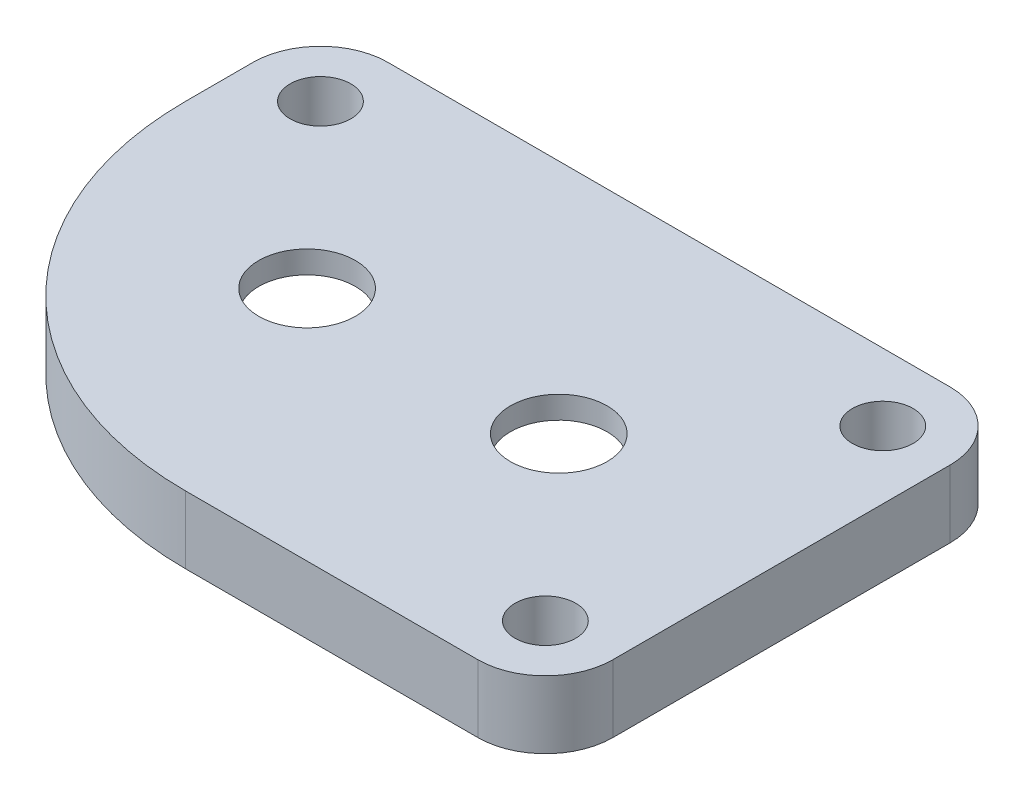
SolidWorks part; units mm, degrees
ref_plane "Front Plane" through (0, 0, 0) normal (0, 0, 1) x (1, 0, 0)
ref_plane "Top Plane" through (0, 0, 0) normal (0, 1, 0) x (1, 0, 0)
ref_plane "Right Plane" through (0, 0, 0) normal (1, 0, 0) x (0, 0, -1)
sketch "Sketch1" plane through (0, 0, 0) normal (0, 1, 0) x (1, 0, 0)
  line L0 (11.19, 0) -> (0, 0) construction
  line L2 (5.095, -10.5) -> (18.095, -10.5)
  line L3 (-9.905, 4.5) -> (-9.905, 7.5)
  line L4 (-6.905, 10.5) -> (18.095, 10.5)
  line L5 (21.095, -7.5) -> (21.095, 7.5)
  line L6 (-9.905, -10.5) -> (21.095, 10.5) construction
  line L7 (-9.905, 10.5) -> (21.095, -10.5) construction
  circle A0 centre (0, 0) radius 2.15
  circle A1 centre (11.19, 0) radius 2.15
  circle A2 centre (-6.905, 7.5) radius 1.35
  circle A3 centre (18.095, 7.5) radius 1.35
  circle A4 centre (18.095, -7.5) radius 1.35
  arc A5 (-9.905, 7.5) -> (-6.905, 10.5) centre (-6.905, 7.5) cw
  arc A6 (18.095, 10.5) -> (21.095, 7.5) centre (18.095, 7.5) cw
  arc A7 (18.095, -10.5) -> (21.095, -7.5) centre (18.095, -7.5) ccw
  arc A8 (5.095, -10.5) -> (-9.905, 4.5) centre (5.095, 4.5) cw
  point P5 (5.595, 0)
  point P16 (0, 0)
  point P17 (0, 0)
  point P18 (0, 0)
  point P19 (23.3808, -10.1698)
  point P20 (18.7065, -11.9323)
  point P21 (23.4575, -12.3921)
  point P34 (1.1802, -9.8565)
  dimension "D2" = 4.3
  dimension "D4" = 2.7
  dimension "D8" = 3
  dimension "D9" = 15
  dimension "D1" = 11.19
  dimension "D3" = 3
  dimension "D5" = 3
  dimension "D6" = 3
  dimension "D7" = 3
  dimension "D10" = 25
  dimension "D11" = 15
extrude "Boss-Extrude1" add sketch "Sketch1" along normal blind 3
sketch "Sketch2" plane through (0, 0, 0) normal (0, -1, 0) x (1, 0, 0)
  line L0 (0, 0) -> (11.19, 0) construction
  line L1 (0, 6.2961) -> (11.19, 6.2961)
  line L2 (0, -6.2961) -> (11.19, -6.2961)
  arc A0 (0, 6.2961) -> (0, -6.2961) centre (0, 0) ccw
  arc A1 (11.19, -6.2961) -> (11.19, 6.2961) centre (11.19, 0) ccw
  point P4 (5.595, 0)
extrude "Cut-Extrude1" cut sketch "Sketch2" against normal blind 2
equation "\"D6@Sketch1\"=\"D5@Sketch1\""
equation "\"D7@Sketch1\"=\"D5@Sketch1\""
